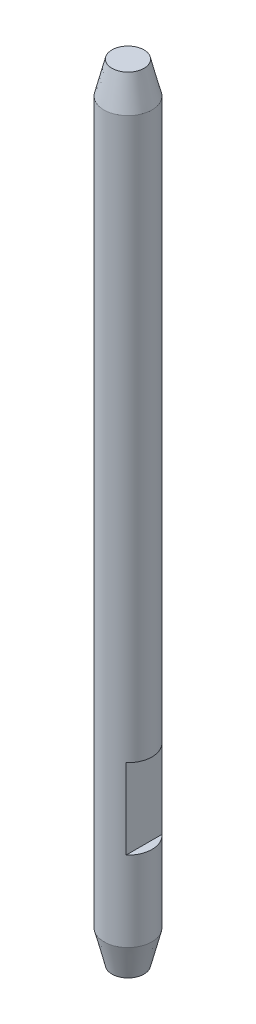
SolidWorks part; units mm, degrees
material "6061-T6 (SS)"
ref_plane "Front Plane" through (0, 0, 0) normal (0, 0, 1) x (1, 0, 0)
ref_plane "Top Plane" through (0, 0, 0) normal (0, 1, 0) x (1, 0, 0)
ref_plane "Right Plane" through (0, 0, 0) normal (1, 0, 0) x (0, 0, -1)
sketch "Sketch1" plane through (0, 0, 0) normal (0, 1, 0) x (1, 0, 0)
  circle A0 centre (0, 0) radius 1.5
  dimension "D1" = 3
extrude "Boss-Extrude1" add sketch "Sketch1" along normal blind 49
chamfer "Chamfer1" distance 0.5 distance2 2 1 edges at (0, 0, 1.5)
chamfer "Chamfer2" distance 2 distance2 0.5 1 edges at (0, 49, 1.5)
ref_plane "Plane1" through (1.5, 0, 0) normal (1, 0, 0) x (0, 0, -1)
sketch "Sketch2" plane through (1.5, 0, 0) normal (1, 0, 0) x (0, 0, -1)
  line L0 (0, 1.65) -> (0, -1.65) construction
  line L1 (-3, 12) -> (3, 12)
  line L2 (-3, 12) -> (-3, 7)
  line L3 (-3, 7) -> (3, 7)
  line L4 (3, 12) -> (3, 7)
  line L5 (-3, 12) -> (3, 7) construction
  line L6 (-3, 7) -> (3, 12) construction
  line L7 (1.65, 0) -> (-1.65, 0) construction
  point P0 (0, 9.5)
  dimension "D1" = 7
  dimension "D2" = 5
  dimension "D3" = 6
extrude "Cut-Extrude1" cut sketch "Sketch2" against normal blind 0.5
